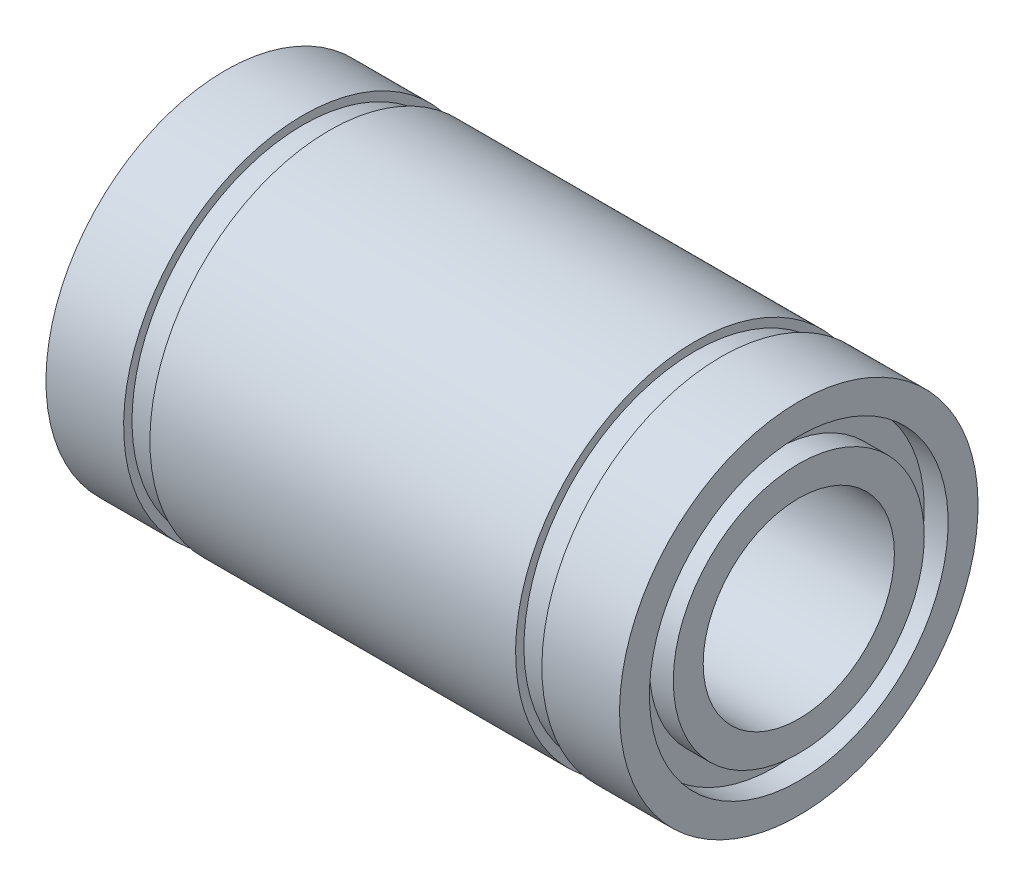
SolidWorks part; units mm, degrees
material "Alliage 1060"
ref_plane "Plano frontal" through (0, 0, 0) normal (0, 0, 1) x (1, 0, 0)
ref_plane "Plano superior" through (0, 0, 0) normal (0, 1, 0) x (1, 0, 0)
ref_plane "Plano direito" through (0, 0, 0) normal (1, 0, 0) x (0, 0, -1)
sketch "Esboço1" plane through (0, 0, 0) normal (0, 0, 1) x (1, 0, 0)
  line L0 (-12, 7.5) -> (-8.75, 7.5)
  line L1 (-8.75, 7.5) -> (-8.75, 7.15)
  line L2 (-8.75, 7.15) -> (-7.65, 7.15)
  line L3 (-7.65, 7.15) -> (-7.65, 7.5)
  line L4 (-7.65, 7.5) -> (7.65, 7.5)
  line L5 (7.65, 7.5) -> (7.65, 7.15)
  line L6 (7.65, 7.15) -> (8.75, 7.15)
  line L7 (8.75, 7.15) -> (8.75, 7.5)
  line L8 (8.75, 7.5) -> (12, 7.5)
  line L9 (12, 7.5) -> (12, 6.25)
  line L10 (12, 4) -> (-12, 4)
  line L11 (-12, 4) -> (-12, 5.25)
  line L12 (0, 4) -> (0, 0) construction
  line L13 (0, 0) -> (-86.5, 0) construction
  line L14 (-12, 6.25) -> (-12, 7.5)
  line L15 (-12, 6.25) -> (-11, 6.25)
  line L16 (12, 5.25) -> (12, 4)
  line L17 (-11, 6.25) -> (-11, 5.25)
  line L18 (-11, 5.25) -> (-12, 5.25)
  line L19 (12, 6.25) -> (11, 6.25)
  line L21 (12, 5.25) -> (11, 5.25)
  line L22 (11, 6.25) -> (11, 5.25)
  dimension "D1" = 24
  dimension "D2" = 17.5
  dimension "D3" = 1.1
  dimension "D4" = 8
  dimension "D5" = 15
  dimension "D6" = 14.3
  dimension "D7" = 1
  dimension "D8" = 1
  dimension "D9" = 1
  dimension "D10" = 1
revolve "Revolution" add sketch "Esboço1" angle 360 about L13
